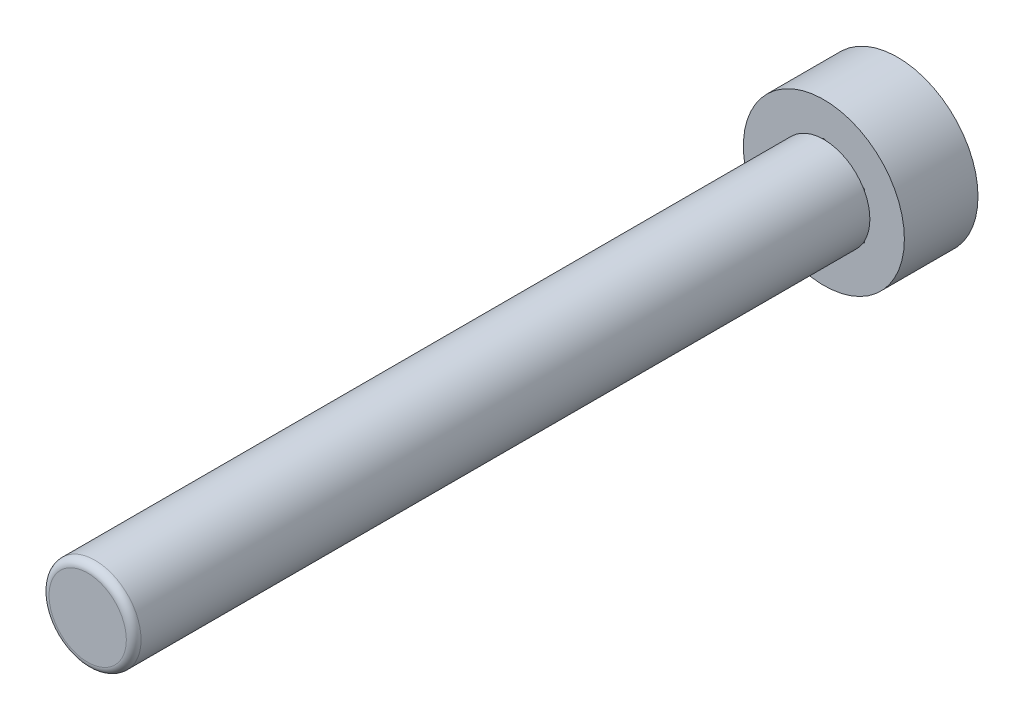
SolidWorks part; units mm, degrees
ref_plane "Front Plane" through (0, 0, 0) normal (0, 0, 1) x (1, 0, 0)
ref_plane "Top Plane" through (0, 0, 0) normal (0, 1, 0) x (1, 0, 0)
ref_plane "Right Plane" through (0, 0, 0) normal (1, 0, 0) x (0, 0, -1)
sketch "Sketch1" plane through (0, 0, 0) normal (0, 0, 1) x (1, 0, 0)
  line L0 (0, 0) -> (0, 8.2431) construction
  line L1 (2.794, 1.6131) -> (0, 3.2262)
  line L2 (0, 3.2262) -> (-2.794, 1.6131)
  line L3 (-2.794, 1.6131) -> (-2.794, -1.6131)
  line L4 (-2.794, -1.6131) -> (0, -3.2262)
  line L5 (0, -3.2262) -> (2.794, -1.6131)
  line L6 (2.794, -1.6131) -> (2.794, 1.6131)
  circle A0 centre (0, 0) radius 2.794 construction
  circle A1 centre (0, 0) radius 5.5562
  dimension "D1" = 5.588
  dimension "D2" = 11.1125
extrude "Boss-Extrude1" add sketch "Sketch1" along normal blind 5.08
sketch "Sketch2" plane through (0, 0, 5.08) normal (0, 0, 1) x (1, 0, 0)
  circle A0 centre (0, 0) radius 3.175
  dimension "D1" = 6.35
extrude "Boss-Extrude2" add sketch "Sketch2" along normal blind 50.8
fillet "Fillet1" radius 0.508 1 edges at (3.175, 0, 55.88)
